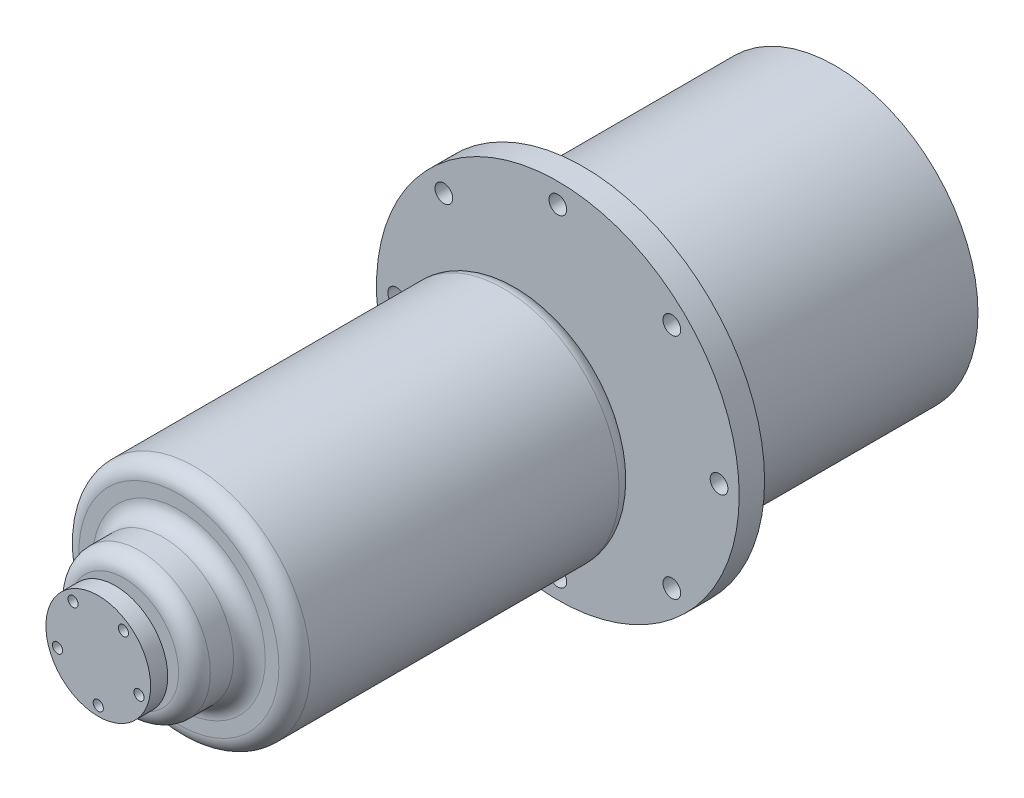
SolidWorks part; units mm, degrees
ref_plane "Front Plane" through (0, 0, 0) normal (0, 0, 1) x (1, 0, 0)
ref_plane "Top Plane" through (0, 0, 0) normal (0, 1, 0) x (1, 0, 0)
ref_plane "Right Plane" through (0, 0, 0) normal (1, 0, 0) x (0, 0, -1)
sketch "Sketch1" plane through (0, 0, 0) normal (0, 0, 1) x (1, 0, 0)
  line L0 (0, 84.8179) -> (0, -86.7057) construction
  line L1 (-97.3585, 0) -> (110.3037, 0) construction
  circle A0 centre (0, 0) radius 57.15
  dimension "D1" = 114.3
extrude "Extrude1" add sketch "Sketch1" along normal mid plane 8
sketch "Sketch3" plane through (0, 0, 4) normal (0, 0, 1) x (1, 0, 0)
  circle A0 centre (0, 0) radius 7.5
  dimension "D1" = 15
extrude "Extrude2" add sketch "Sketch3" along normal blind 12.166
sketch "Sketch4" plane through (0, 0, 16.166) normal (0, 0, 1) x (1, 0, 0)
  circle A0 centre (0, 0) radius 36.5
  dimension "D1" = 73
extrude "Extrude3" add sketch "Sketch4" along normal blind 107.24
sketch "Sketch5" plane through (0, 0, 123.406) normal (0, 0, 1) x (1, 0, 0)
  circle A0 centre (0, 0) radius 22.225
  dimension "D1" = 44.45
extrude "Extrude4" add sketch "Sketch5" along normal blind 17.3228
sketch "Sketch6" plane through (0, 0, 140.7288) normal (0, 0, 1) x (1, 0, 0)
  circle A0 centre (0, 0) radius 9.525
  dimension "D1" = 19.05
extrude "Extrude5" add sketch "Sketch6" along normal blind 2.7021
sketch "Sketch7" plane through (0, 0, 143.4309) normal (0, 0, 1) x (1, 0, 0)
  circle A0 centre (0, 0) radius 16.5
  dimension "D1" = 33
extrude "Extrude6" add sketch "Sketch7" along normal blind 5.3848
sketch "Sketch8" plane through (0, 0, 148.8157) normal (0, 0, 1) x (1, 0, 0)
  line L0 (0, 0) -> (-14.2331, 19.5901) construction
  line L1 (0, 0) -> (15.2254, 20.956) construction
  line L2 (0, 0) -> (18.3713, -5.9692) construction
  line L3 (0, 0) -> (0, -19.9096) construction
  line L4 (0, 0) -> (-20.1546, -6.5486) construction
  circle A0 centre (0, 0) radius 13.5 construction
  circle A1 centre (-7.9351, 10.9217) radius 1.6
  circle A2 centre (7.9351, 10.9217) radius 1.6
  circle A3 centre (12.8393, -4.1717) radius 1.6
  circle A4 centre (0, -13.5) radius 1.6
  circle A5 centre (-12.8393, -4.1717) radius 1.6
  dimension "D1" = 27
  dimension "D6" = 3.2
  dimension "D2" = 72
  dimension "D3" = 72
  dimension "D4" = 72
  dimension "D5" = 72
extrude "Cut-Extrude1" cut sketch "Sketch8" against normal blind 5.3848
sketch "Sketch10" plane through (0, 0, -4) normal (0, 0, -1) x (-1, 0, 0)
  line L0 (0, 62.7428) -> (0, -62.7428) construction
  line L1 (-61.7117, 0) -> (61.7117, 0) construction
  line L2 (46.601, 46.601) -> (-46.601, -46.601) construction
  line L3 (-47.2013, 47.2013) -> (47.2013, -47.2013) construction
  circle A1 centre (0, 0) radius 50.8 construction
  circle A2 centre (0, 50.8) radius 2.79
  circle A3 centre (35.921, 35.921) radius 2.79
  circle A4 centre (50.8, 0) radius 2.79
  circle A5 centre (35.921, -35.921) radius 2.79
  circle A6 centre (0, -50.8) radius 2.79
  circle A7 centre (-35.921, -35.921) radius 2.79
  circle A8 centre (-50.8, 0) radius 2.79
  circle A9 centre (-35.921, 35.921) radius 2.79
  dimension "D3" = 101.6
  dimension "D4" = 5.58
  dimension "D1" = 45
  dimension "D2" = 45
extrude "Cut-Extrude2" cut sketch "Sketch10" against normal up to surface (8 mm away) up to face at (57.15, 0, 4)
sketch "Sketch11" plane through (0, 0, -4) normal (0, 0, -1) x (-1, 0, 0)
  circle A0 centre (0, 0) radius 45
  dimension "D1" = 90
extrude "Extrude7" add sketch "Sketch11" along normal blind 79.4
fillet "Fillet1" radius 5 4 edges at (22.225, 0, 140.7288) (22.225, 0, 123.406) (36.5, 0, 123.406) (36.5, 0, 16.166)
